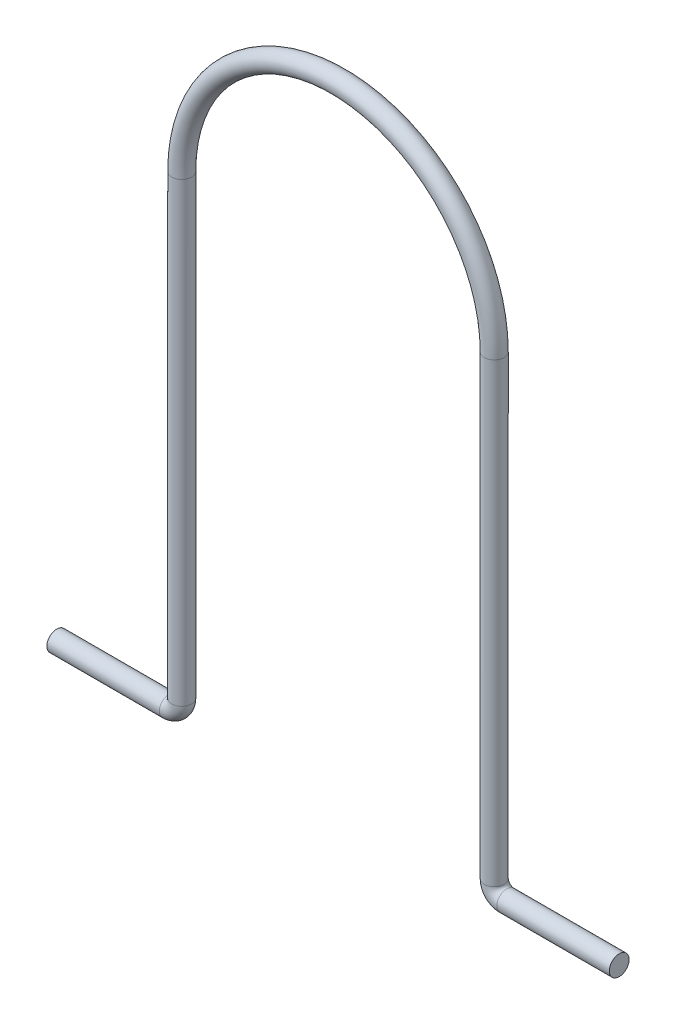
SolidWorks part; units mm, degrees
ref_plane "Front Plane" through (0, 0, 0) normal (0, 0, 1) x (1, 0, 0)
ref_plane "Top Plane" through (0, 0, 0) normal (0, 1, 0) x (1, 0, 0)
ref_plane "Right Plane" through (0, 0, 0) normal (1, 0, 0) x (0, 0, -1)
sketch "Sketch1" plane through (0, 0, 0) normal (0, 0, 1) x (1, 0, 0)
  line L0 (0, 0) -> (18, 0)
  line L1 (20, 2) -> (20, 75)
  line L3 (70, 75) -> (70, 2)
  line L4 (72, 0) -> (90, 0)
  arc A0 (70, 75) -> (20, 75) centre (45, 75) ccw
  arc A1 (70, 2) -> (72, 0) centre (72, 2) ccw
  arc A2 (18, 0) -> (20, 2) centre (18, 2) ccw
  point P10 (70, 0)
  point P13 (20, 0)
  dimension "D1" = 75
  dimension "D4" = 25
  dimension "D5" = 2
  dimension "D2" = 20
  dimension "D3" = 20
sketch "Sketch2" plane through (0, 0, 0) normal (1, 0, 0) x (0, 0, -1)
  circle A0 centre (0, 0) radius 1.5875
  dimension "D1" = 3.175
sweep "Sweep1" add profiles "Sketch2" path "Sketch1"
